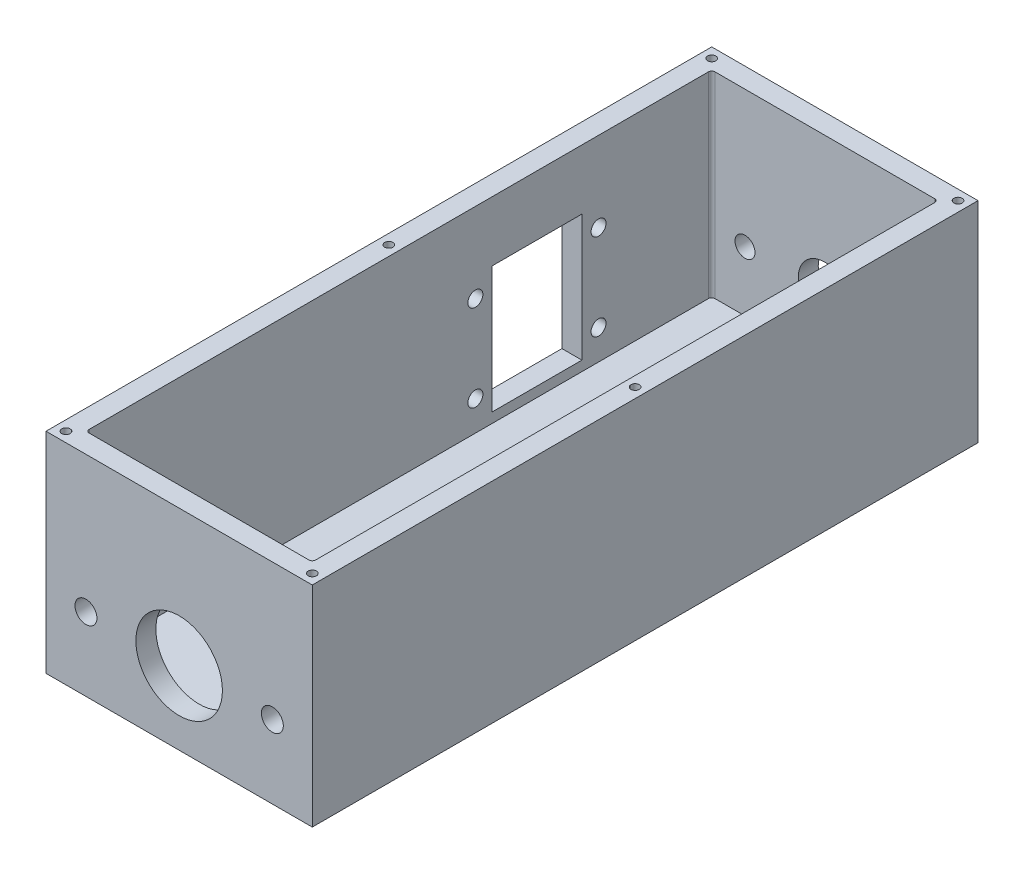
SolidWorks part; units mm, degrees
material "1060 合金"
ref_plane "前视基准面" through (0, 0, 0) normal (0, 0, 1) x (1, 0, 0)
ref_plane "上视基准面" through (0, 0, 0) normal (0, 1, 0) x (1, 0, 0)
ref_plane "右视基准面" through (0, 0, 0) normal (1, 0, 0) x (0, 0, -1)
sketch "草图1" plane through (0, 0, 0) normal (0, 0, 1) x (1, 0, 0)
  line L1 (-40, -24) -> (40, -24)
  line L2 (-40, -24) -> (-40, 24)
  line L3 (-40, 24) -> (40, 24)
  line L4 (40, -24) -> (40, 24)
  line L5 (-40, -24) -> (40, 24) construction
  line L6 (-40, 24) -> (40, -24) construction
  point P0 (0, 0)
  dimension "D1" = 80
  dimension "D2" = 48
extrude "凸台-拉伸1" add sketch "草图1" against normal blind 200
sketch "草图2" plane through (0, 24, 0) normal (0, 1, 0) x (1, 0, 0)
  line L0 (-34, 193) -> (-34, 7)
  line L1 (-33, 6) -> (33, 6)
  line L2 (34, 7) -> (34, 193)
  line L3 (33, 194) -> (-33, 194)
  line L4 (-40, 0) -> (40, 0)
  line L5 (40, 0) -> (40, 200)
  line L6 (40, 200) -> (-40, 200)
  line L7 (-40, 200) -> (-40, 0)
  line L8 (-40, 0) -> (40, 0)
  line L9 (40, 0) -> (40, 200)
  line L10 (40, 200) -> (-40, 200)
  line L11 (-40, 200) -> (-40, 0)
  line L12 (-34, 6) -> (34, 6) construction
  line L13 (34, 6) -> (34, 194) construction
  line L14 (-34, 194) -> (-34, 6) construction
  line L15 (34, 194) -> (-34, 194) construction
  arc A0 (33, 6) -> (34, 7) centre (33, 7) ccw
  arc A1 (-34, 7) -> (-33, 6) centre (-33, 7) ccw
  arc A2 (34, 193) -> (33, 194) centre (33, 193) ccw
  arc A3 (-34, 193) -> (-33, 194) centre (-33, 193) cw
  dimension "D3" = 1
  dimension "D1" = 0
  dimension "D2" = 6
extrude "切除-拉伸1" cut sketch "草图2" against normal blind 44 contours A3 L0 A1 L1 A0 L2 A2 L3
sketch "草图3" plane through (0, 0, 0) normal (0, 0, 1) x (1, 0, 0)
  line L0 (0, 0) -> (0, 37.0041) construction
  line L1 (-40, -26) -> (40, -26) construction
  line L2 (-40, 24) -> (-40, -24) construction
  line L3 (40, -24) -> (40, 24) construction
  line L5 (40, 24) -> (-40, 24) construction
  line L6 (-34, -26) -> (40, -26) construction
  line L9 (0, -2) -> (0, 24) construction
  line L10 (-28, -2) -> (28, -2) construction
  circle A0 centre (-28, -2) radius 3.3
  circle A1 centre (0, -2) radius 13
  circle A2 centre (28, -2) radius 3.3
  dimension "D2" = 6.6
  dimension "D3" = 26
  dimension "D4" = 6.6
  dimension "D1" = 26
  dimension "D5" = 24
  dimension "D6" = 28
  dimension "D7" = 28
extrude "切除-拉伸2" cut sketch "草图3" against normal blind 10
sketch "草图4" plane through (-40, 0, 0) normal (-1, 0, 0) x (0, 0, 1)
  line L0 (-128, -17) -> (-155, -17)
  line L1 (-128, -17) -> (-128, 21)
  line L2 (-128, 21) -> (-155, 21)
  line L3 (-155, -17) -> (-155, 21)
  line L4 (-141.5, -1.9135) -> (-141.5, 22.4271) construction
  line L5 (-200, 24) -> (0, 24) construction
  line L6 (-200, 24) -> (-200, -24) construction
  circle A0 centre (-123, -11) radius 2.25
  circle A1 centre (-123, 15) radius 2.25
  circle A2 centre (-160, 15) radius 2.25
  circle A3 centre (-160, -11) radius 2.25
  dimension "D1" = 4.5
  dimension "D2" = 4.5
  dimension "D3" = 38
  dimension "D4" = 6
  dimension "D5" = 5
  dimension "D6" = 6
  dimension "D7" = 5
  dimension "D8" = 27
  dimension "D9" = 3
  dimension "D10" = 58.5
extrude "切除-拉伸3" cut sketch "草图4" against normal blind 10
sketch "草图5" plane through (0, 0, -200) normal (0, 0, -1) x (-1, 0, 0)
  line L0 (0, -25.8214) -> (0, 19.1786) construction
  line L1 (0, 24) -> (0, 39.9128) construction
  line L2 (0, -2) -> (24, -2) construction
  line L5 (-40, 24) -> (40, 24) construction
  circle A0 centre (0, -2) radius 8
  circle A1 centre (24, -2) radius 3
  circle A2 centre (-24, -2) radius 3
  dimension "D1" = 16
  dimension "D3" = 6
  dimension "D2" = 26
  dimension "D4" = 24
extrude "切除-拉伸4" cut sketch "草图5" against normal blind 10
sketch "草图6" plane through (0, -20, 0) normal (0, 1, 0) x (1, 0, 0)
  line L0 (-16, 115) -> (-16, 168) construction
  line L1 (-16, 141.5) -> (-23.7867, 141.5) construction
  line L2 (-34, 193) -> (-34, 7) construction
  line L3 (33, 194) -> (-33, 194) construction
  circle A0 centre (-16, 168) radius 3.5
  circle A1 centre (-16, 115) radius 3.5
  dimension "D2" = 7
  dimension "D5" = 7
  dimension "D1" = 53
  dimension "D3" = 18
  dimension "D4" = 52.5
extrude "切除-拉伸5" cut sketch "草图6" against normal blind 10
sketch "草图8" plane through (0, 24, 0) normal (0, 1, 0) x (1, 0, 0)
  line L0 (-40, 0) -> (40, 0)
  line L1 (-40, 0) -> (-40, 200)
  line L2 (40, 0) -> (40, 200)
  line L3 (-40, 200) -> (40, 200)
  line L5 (-34, 193) -> (-34, 7) construction
  line L6 (34, 7) -> (34, 193) construction
  line L7 (-33, 6) -> (33, 6) construction
  line L8 (33, 194) -> (-33, 194) construction
  line L9 (-33, 6) -> (33, 6)
  line L10 (34, 7) -> (34, 193)
  line L11 (-34, 193) -> (-34, 7)
  line L12 (33, 194) -> (-33, 194)
  arc A0 (34, 193) -> (33, 194) centre (33, 193) ccw construction
  arc A1 (-33, 194) -> (-34, 193) centre (-33, 193) ccw construction
  arc A2 (-34, 7) -> (-33, 6) centre (-33, 7) ccw construction
  arc A3 (33, 6) -> (34, 7) centre (33, 7) ccw construction
  arc A4 (-34, 7) -> (-33, 6) centre (-33, 7) ccw
  arc A5 (33, 6) -> (34, 7) centre (33, 7) ccw
  arc A6 (-33, 194) -> (-34, 193) centre (-33, 193) ccw
  arc A7 (34, 193) -> (33, 194) centre (33, 193) ccw
extrude "凸台-拉伸2" add sketch "草图8" along normal blind 15
sketch "草图10" plane through (0, 39, 0) normal (0, 1, 0) x (1, 0, 0)
  line L0 (0, 0) -> (0, 200) construction
  line L1 (40, 200) -> (-40, 200) construction
  line L2 (-40, 0) -> (40, 0) construction
  line L3 (-40, 200) -> (-40, 0) construction
  point P0 (-37, 197)
  point P1 (-37, 100)
  point P2 (-37, 3)
  point P12 (-40, 100)
  point P13 (37, 3)
  point P14 (37, 100)
  point P15 (37, 197)
  dimension "D1" = 3
  dimension "D2" = 3
  dimension "D3" = 3
  dimension "D4" = 100
hole_wizard "M3 螺纹孔1" positions "3D草图1" profile "草图11" tap size "M3" standard "GB"
sketch3d "3D草图1"
  point P0 (-37, 39, -100)
  point P3 (37, 39, -100)
  point P6 (37, 39, -3)
  point P9 (-37, 39, -3)
  point P12 (-37, 39, -197)
  point P15 (37, 39, -197)
sketch "草图11" plane through (-37, 39, -100) normal (1, 0, 0) x (0, 0, 1)
  line L0 (0, 0) -> (0, 8.2511)
  line L1 (0, 8.2511) -> (1.25, 7.5)
  line L2 (1.25, 7.5) -> (1.25, 0)
  line L5 (1.25, 0) -> (0, 0)
  line L10 (0, 8.2511) -> (-1.25, 7.5) construction
  line L11 (0, -6.35) -> (0, 107.95) construction
  dimension "螺纹孔钻头直径" = 2.5
  dimension "螺纹孔钻头深度" = 7.5
  dimension "导头角度" = 118
cosmetic thread "孔螺蚊线1" parameters "D1"=6, "D2"=3
cosmetic thread "孔螺蚊线2" parameters "D1"=6, "D2"=3
cosmetic thread "孔螺蚊线3" parameters "D1"=6, "D2"=3
cosmetic thread "孔螺蚊线4" parameters "D1"=6, "D2"=3
cosmetic thread "孔螺蚊线5" parameters "D1"=6, "D2"=3
cosmetic thread "孔螺蚊线6" parameters "D1"=6, "D2"=3
